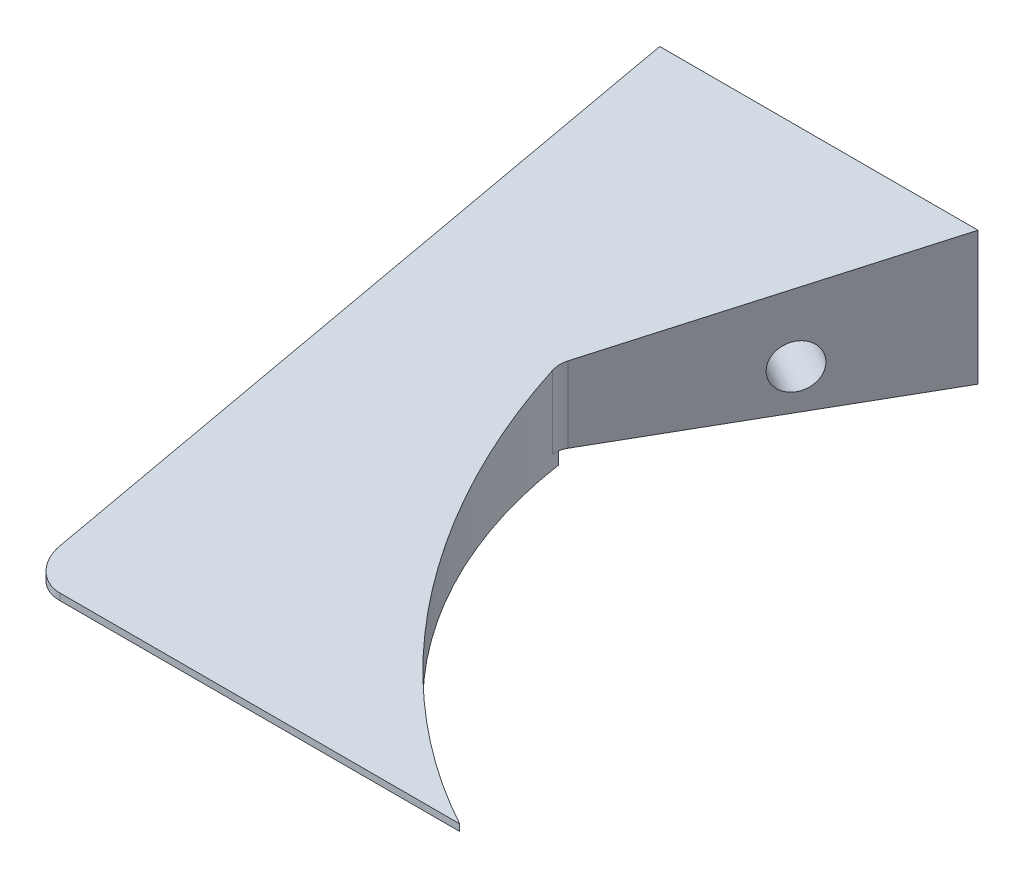
SolidWorks part; units mm, degrees
material "AISI 4130 Aço, normalizado a 870C"
ref_plane "Plano frontal" through (0, 0, 0) normal (0, 0, 1) x (1, 0, 0)
ref_plane "Plano superior" through (0, 0, 0) normal (0, 1, 0) x (1, 0, 0)
ref_plane "Plano direito" through (0, 0, 0) normal (1, 0, 0) x (0, 0, -1)
sketch "Esboço1" plane through (0, 0, 0) normal (0, 0, 1) x (1, 0, 0)
  line L1 (-65, 11) -> (65, 11)
  line L2 (-65, 11) -> (-65, -11)
  line L3 (-65, -11) -> (65, -11)
  line L4 (65, 11) -> (65, -11)
  line L5 (-65, 11) -> (65, -11) construction
  line L6 (-65, -11) -> (65, 11) construction
  point P0 (0, 0)
  dimension "D1" = 130
  dimension "D2" = 22
extrude "Ressalto-extrusão1" add sketch "Esboço1" along normal blind 95
sketch "Esboço2" plane through (0, 11, 0) normal (0, 1, 0) x (1, 0, 0)
  line L0 (65, 0) -> (-17.25, 0)
  line L2 (-65, -95) -> (-65, 0) construction
  line L3 (-40.2, -40) -> (-17.25, 0)
  line L4 (65, 0) -> (-65, 0) construction
  line L10 (65, -95) -> (-65, -95) construction
  line L11 (0, -95) -> (65, -95)
  line L12 (65, -95) -> (65, 0)
  arc A1 (0, -95) -> (-40.2, -40) centre (32.4564, -29.086) cw
  dimension "D4" = 73.4716
  dimension "D5" = 40
  dimension "D1" = 47.75
  dimension "D2" = 24.8
  dimension "D3" = 65
extrude "Corte-extrusão2" cut sketch "Esboço2" against normal up to next contours L3 L0 L12 L11 A1
sketch "Esboço13" plane through (-65, 0, 0) normal (-1, 0, 0) x (0, 0, 1)
  line L0 (0, 11) -> (95, -10)
  line L1 (95, 11) -> (95, -11) construction
  dimension "D1" = 1
extrude "Corte-extrusão4" cut sketch "Esboço13" against normal through all and the other way through all
hole_wizard "Broca de rosquear de cano para tarraxa de 1/84" positions "Esboço14" profile "Esboço15" hole size "1/8" standard "Ansi Inch"
sketch "Esboço14" plane through (-65, 0, 0) normal (-1, 0, 0) x (0, 0, 1)
  line L0 (0, 11) -> (0, -11) construction
  line L1 (95, -11) -> (0, -11) construction
  point P0 (20, -3)
  dimension "D1" = 20
  dimension "D2" = 8
sketch "Esboço15" plane through (-65, -3, 20) normal (0, 1, 0) x (0, 0, 1)
  line L0 (0, 0) -> (0, 11.9768)
  line L1 (0, 11.9768) -> (3.29, 10)
  line L2 (3.29, 10) -> (3.29, 0)
  line L5 (3.29, 0) -> (0, 0)
  line L10 (0, 11.9768) -> (-3.29, 10) construction
  line L11 (0, -6.35) -> (0, 107.95) construction
  dimension "Hole Dia." = 6.58
  dimension "Hole Depth" = 10
  dimension "Drill Angle" = 118
hole_wizard "Broca de rosquear de cano para tarraxa de 1/85" positions "Esboço16" profile "Esboço17" hole size "1/8" standard "Ansi Inch"
sketch "Esboço16" plane through (-12.9778, 0, -7.446) normal (0.8674, 0, 0.4977) x (0.4977, 0, -0.8674)
  line L0 (-8.5846, -11) -> (-8.5846, 11) construction
  line L1 (-8.5846, -11) -> (-54.7008, -11) construction
  point P0 (-28.5846, -3)
  dimension "D1" = 20
  dimension "D2" = 8
sketch "Esboço17" plane through (-27.2031, -3, 17.3475) normal (0, 1, 0) x (0.4977, 0, -0.8674)
  line L0 (0, 0) -> (0, 11.9768)
  line L1 (0, 11.9768) -> (3.29, 10)
  line L2 (3.29, 10) -> (3.29, 0)
  line L5 (3.29, 0) -> (0, 0)
  line L10 (0, 11.9768) -> (-3.29, 10) construction
  line L11 (0, -6.35) -> (0, 107.95) construction
  dimension "Hole Dia." = 6.58
  dimension "Hole Depth" = 10
  dimension "Drill Angle" = 118
fillet "Filete2" radius 5 1 edges at (-65, -10.5, 95)
sketch "Esboço38" plane through (0, 0, 0) normal (0, 0, -1) x (-1, 0, 0)
  line L0 (17.25, -9) -> (65, -9)
  line L1 (17.25, -11) -> (17.25, 11) construction
  line L2 (65, 11) -> (65, -11) construction
  line L3 (65, -9) -> (65, -11)
  line L4 (65, -11) -> (17.25, -11)
  line L5 (0, -11) -> (40.2, -11) construction
  line L6 (65, -11) -> (17.25, -11) construction
  line L7 (17.25, -11) -> (17.25, -9)
  dimension "D1" = 2
extrude "Corte-extrusão9" cut sketch "Esboço38" against normal blind 40
fillet "Filete3" radius 3 1 edges at (-40.2, -3.4211, 40)
